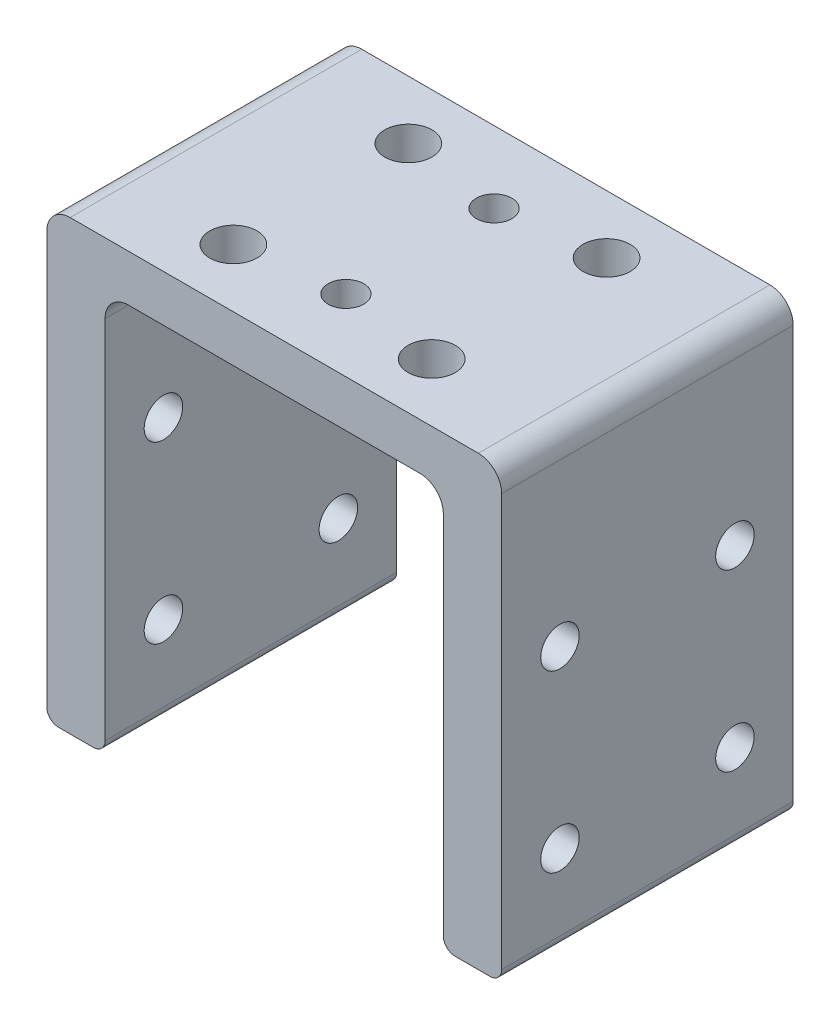
SolidWorks part; units mm, degrees
material "6063-T5"
ref_plane "前视基准面" through (0, 0, 0) normal (0, 0, 1) x (1, 0, 0)
ref_plane "上视基准面" through (0, 0, 0) normal (0, 1, 0) x (1, 0, 0)
ref_plane "右视基准面" through (0, 0, 0) normal (1, 0, 0) x (0, 0, -1)
other "Configuration Table"
sketch "草图1" plane through (0, 0, 0) normal (0, 0, 1) x (1, 0, 0)
  line L1 (-19.5, -24.5) -> (19.5, -24.5)
  line L2 (-19.5, -24.5) -> (-19.5, 24.5)
  line L3 (-19.5, 24.5) -> (19.5, 24.5)
  line L4 (19.5, -24.5) -> (19.5, 24.5)
  line L5 (-19.5, -24.5) -> (19.5, 24.5) construction
  line L6 (-19.5, 24.5) -> (19.5, -24.5) construction
  point P0 (0, 0)
  dimension "D1" = 39
  dimension "D2" = 49
extrude "凸台-拉伸1" add sketch "草图1" along normal blind 25
sketch "草图3" plane through (0, 0, 25) normal (0, 0, 1) x (1, 0, 0)
  line L0 (-14.5, -24.5) -> (-14.5, 20.5)
  line L1 (-19.5, -24.5) -> (19.5, -24.5) construction
  line L2 (-14.5, 20.5) -> (14.5, 20.5)
  line L3 (14.5, 20.5) -> (14.5, -24.5)
  line L4 (14.5, -24.5) -> (-14.5, -24.5)
  line L5 (0, 0) -> (0, -24.5) construction
  line L6 (19.5, 24.5) -> (-19.5, 24.5) construction
  dimension "D1" = 4
  dimension "D2" = 29
extrude "切除-拉伸1" cut sketch "草图3" against normal blind 25
sketch "草图4" plane through (0, 20.5, 0) normal (0, -1, 0) x (1, 0, 0)
  line L0 (0, 0) -> (0, 25) construction
  line L1 (14.5, 0) -> (-14.5, 0) construction
  line L2 (14.5, 25) -> (-14.5, 25) construction
  line L3 (19.5, 12.5) -> (-19.5, 12.5) construction
  line L4 (19.5, 25) -> (19.5, 0) construction
  line L5 (-19.5, 25) -> (-19.5, 0) construction
  circle A0 centre (0, 18.85) radius 1.525
  circle A1 centre (0, 6.15) radius 1.525
  dimension "D1" = 3.05
  dimension "D2" = 12.7
sketch "草图5" plane through (0, 0, 25) normal (0, 0, 1) x (1, 0, 0)
  line L0 (19.5, -24.5) -> (19.5, 24.5) construction
  line L1 (-19.5, -24.5) -> (19.5, -24.5)
  line L2 (-19.5, -24.5) -> (-19.5, -19.5)
  line L3 (-19.5, -19.5) -> (19.5, -19.5)
  line L4 (19.5, -24.5) -> (19.5, -19.5)
  dimension "D1" = 5
extrude "切除-拉伸3" cut sketch "草图5" against normal through all both and the other way through all
sketch "草图7" plane through (0, 20.5, 0) normal (0, -1, 0) x (1, 0, 0)
  line L0 (0, 12.5) -> (14.5, 12.5) construction
  line L1 (-8.5, 5) -> (8.5, 5) construction
  line L2 (-8.5, 5) -> (-8.5, 20) construction
  line L3 (-8.5, 20) -> (8.5, 20) construction
  line L4 (8.5, 5) -> (8.5, 20) construction
  line L5 (-8.5, 5) -> (8.5, 20) construction
  line L6 (-8.5, 20) -> (8.5, 5) construction
  line L7 (14.5, 0) -> (14.5, 25) construction
  circle A0 centre (-8.5, 20) radius 2.025
  circle A1 centre (-8.5, 5) radius 2.025
  circle A2 centre (8.5, 5) radius 2.025
  circle A3 centre (8.5, 20) radius 2.025
  point P0 (0, 12.5)
  dimension "D2" = 4.05
  dimension "D1" = 17
  dimension "D3" = 15
sketch "草图12" plane through (14.5, 0, 0) normal (-1, 0, 0) x (0, 0, 1)
  line L0 (0, -19.5) -> (25, -19.5) construction
  line L1 (5, -6.35) -> (20, -6.35) construction
  line L2 (5, -6.35) -> (5, 8.65) construction
  line L3 (5, 8.65) -> (20, 8.65) construction
  line L4 (20, -6.35) -> (20, 8.65) construction
  line L5 (5, -6.35) -> (20, 8.65) construction
  line L6 (5, 8.65) -> (20, -6.35) construction
  line L7 (12.5, -19.5) -> (12.5, 1.15) construction
  circle A0 centre (20, 8.65) radius 2.025
  circle A1 centre (5, 8.65) radius 2.025
  circle A2 centre (5, -6.35) radius 2.025
  circle A3 centre (20, -6.35) radius 2.025
  point P0 (12.5, 1.15)
  dimension "D2" = 4.05
  dimension "D1" = 20.65
  dimension "D3" = 15
  dimension "D4" = 15
sketch "草图17" plane through (-19.5, 0, 0) normal (-1, 0, 0) x (0, 0, 1)
  circle A1 centre (20, -6.35) radius 2.025
  circle A2 centre (20, -6.35) radius 2.025
  circle A3 centre (5, -6.35) radius 2.025
  circle A4 centre (5, -6.35) radius 2.025
  circle A5 centre (5, 8.65) radius 2.025
  circle A6 centre (5, 8.65) radius 2.025
  circle A7 centre (20, 8.65) radius 2.025
  circle A8 centre (20, 8.65) radius 2.025
  dimension "D1" = 0
  dimension "D2" = 0
  dimension "D3" = 0
  dimension "D4" = 0
hole_wizard "M4 螺纹孔4" positions "3D草图5" profile "草图19" tap size "M4" standard "GB" end condition through all
sketch3d "3D草图5"
  point P0 (-19.5, 8.65, 5)
  point P3 (-19.5, 8.65, 20)
  point P6 (-19.5, -6.35, 20)
  point P9 (-19.5, -6.35, 5)
sketch "草图19" plane through (-19.5, 8.65, 5) normal (0, 1, 0) x (0, 0, 1)
  line L0 (0, 0) -> (0, 39)
  line L1 (0, 39) -> (1.65, 39)
  line L2 (1.65, 39) -> (1.65, 0)
  line L5 (1.65, 0) -> (0, 0)
  line L11 (0, -6.35) -> (0, 107.95) construction
  dimension "通孔螺纹孔钻头直径" = 3.3
  dimension "通孔螺纹孔钻头深度" = 39
cosmetic thread "孔螺蚊线15" parameters "D2"=4
cosmetic thread "孔螺蚊线16" parameters "D2"=4
cosmetic thread "孔螺蚊线17" parameters "D2"=4
cosmetic thread "孔螺蚊线18" parameters "D2"=4
sketch "草图20" plane through (0, 0, 25) normal (0, 0, 1) x (1, 0, 0)
  line L0 (19.5, -19.5) -> (19.5, 24.5) construction
  line L1 (-19.5, -19.5) -> (19.5, -19.5)
  line L2 (-19.5, -19.5) -> (-19.5, -13.85)
  line L3 (-19.5, -13.85) -> (19.5, -13.85)
  line L4 (19.5, -19.5) -> (19.5, -13.85)
  dimension "D1" = 5.65
extrude "切除-拉伸5" cut sketch "草图20" against normal through all both
extrude "切除-拉伸7" cut sketch "草图7" against normal blind 10
fillet "圆角1" radius 2 4 edges at (14.5, 20.5, 12.5) (-14.5, 20.5, 12.5) (19.5, 24.5, 12.5) (-19.5, 24.5, 12.5)
fillet "圆角2" radius 1 4 edges at (-19.5, -13.85, 12.5) (-14.5, -13.85, 12.5) (14.5, -13.85, 12.5) (19.5, -13.85, 12.5)
sketch "草图21" plane through (0, 24.5, 0) normal (0, 1, 0) x (1, 0, 0)
  circle A0 centre (0, -6.15) radius 1.525
  circle A1 centre (0, -18.85) radius 1.525
  dimension "D1" = 3.05
extrude "切除-拉伸8" cut sketch "草图21" against normal blind 10
